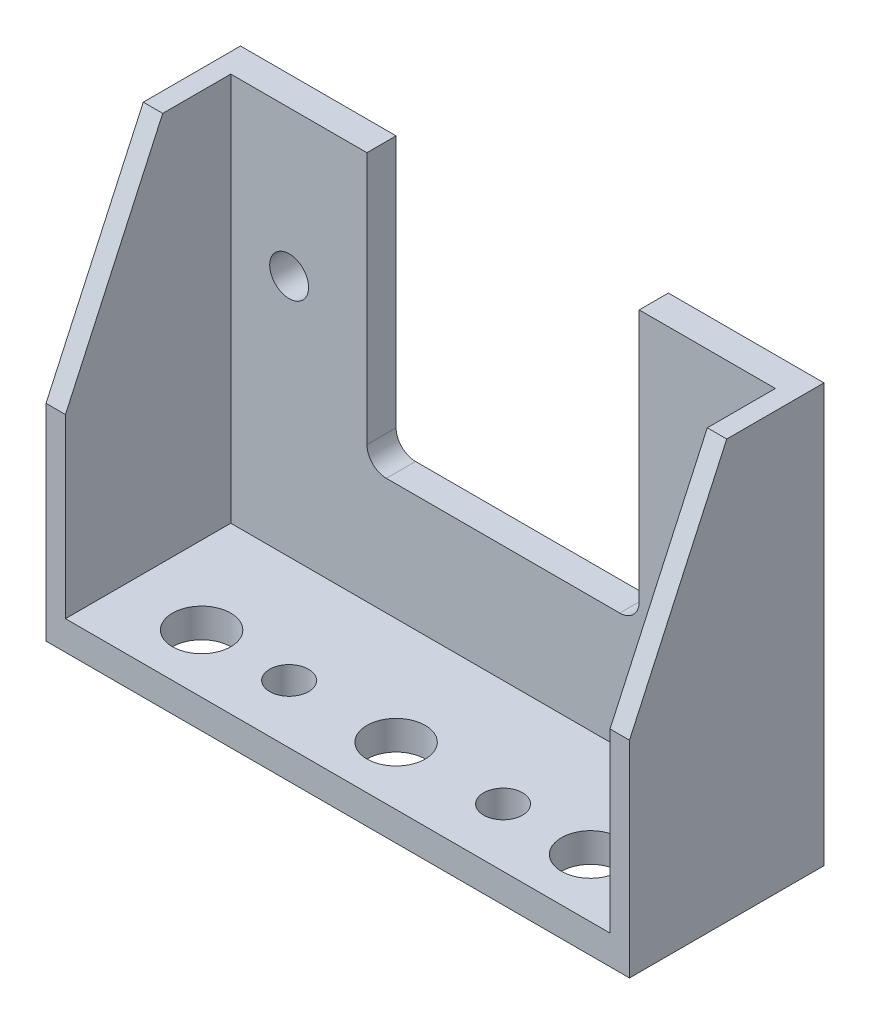
SolidWorks part; units mm, degrees
ref_plane "Front Plane" through (0, 0, 0) normal (0, 0, 1) x (1, 0, 0)
ref_plane "Top Plane" through (0, 0, 0) normal (0, 1, 0) x (1, 0, 0)
ref_plane "Right Plane" through (0, 0, 0) normal (1, 0, 0) x (0, 0, -1)
sketch "Sketch1" plane through (0, 0, 0) normal (0, 1, 0) x (1, 0, 0)
  line L1 (-15, 5) -> (15, 5)
  line L2 (-15, 5) -> (-15, -5)
  line L3 (-15, -5) -> (15, -5)
  line L4 (15, 5) -> (15, -5)
  line L5 (-15, 5) -> (15, -5) construction
  line L6 (-15, -5) -> (15, 5) construction
  circle A0 centre (0, -2) radius 1.5
  point P0 (0, 0)
  dimension "D3" = 3
  dimension "D1" = 30
  dimension "D2" = 10
  dimension "D4" = 3
extrude "Boss-Extrude1" add sketch "Sketch1" along normal mid plane 1.5
sketch "Sketch2" plane through (0, 0.75, 0) normal (0, 1, 0) x (1, 0, 0)
  line L0 (-15, 5) -> (-15, -5) construction
  line L1 (-15, -5) -> (15, -5) construction
  line L2 (0, -0.825) -> (0, 0.825) construction
  circle A0 centre (-10, -2) radius 1.5
  circle A1 centre (10, -2) radius 1.5
  circle A2 centre (-5.5, -2) radius 1
  circle A3 centre (5.5, -2) radius 1
  point P12 (0, 0)
  dimension "D1" = 3
  dimension "D4" = 2
  dimension "D2" = 5
  dimension "D3" = 3
  dimension "D5" = 9.5
extrude "Cut-Extrude1" cut sketch "Sketch2" against normal blind 1.5
sketch "Sketch3" plane through (0, 0, 0) normal (0, 0, 1) x (1, 0, 0)
  line L0 (-15, 0.75) -> (-15, -0.75) construction
  line L1 (15, 20.75) -> (-15, 20.75)
  line L2 (15, 20.75) -> (15, 0.75)
  line L3 (15, 0.75) -> (-15, 0.75)
  line L4 (-15, 20.75) -> (-15, 0.75)
  line L5 (15, 20.75) -> (-15, 0.75) construction
  line L6 (15, 0.75) -> (-15, 20.75) construction
  line L7 (15, 0.75) -> (-15, 0.75) construction
  line L9 (-7, 20.75) -> (7, 20.75)
  line L10 (-7, 20.75) -> (-7, 6.75)
  line L11 (-7, 6.75) -> (7, 6.75)
  line L12 (7, 20.75) -> (7, 6.75)
  point P0 (0, 10.75)
  dimension "D1" = 20
  dimension "D2" = 14
  dimension "D3" = 8
  dimension "D4" = 8
extrude "Boss-Extrude3" add sketch "Sketch3" along normal mid plane 1.5 from offset 4.25 contours L1 L12 L11 L10 L4 L3 L2 offset against normal yes
sketch "Sketch4" plane through (0, 0, 0) normal (0, 0, 1) x (1, 0, 0)
  line L0 (-7, 20.75) -> (-15, 20.75) construction
  line L1 (-15, 20.75) -> (-15, 0.75) construction
  line L2 (0, -5.5) -> (0, 5.5) construction
  circle A0 centre (-11, 13.25) radius 1
  circle A1 centre (11, 13.25) radius 1
  dimension "D1" = 2
  dimension "D2" = 7.5
  dimension "D3" = 4
extrude "Cut-Extrude2" cut sketch "Sketch4" against normal blind 10
fillet "Fillet1" radius 1 2 edges at (7, 6.75, -4.25) (-7, 6.75, -4.25)
sketch "Sketch7" plane through (0, 0, 0) normal (1, 0, 0) x (0, 0, -1)
  line L0 (3.5, 20.75) -> (0, 20.75)
  line L1 (3.5, 20.75) -> (-5, 20.75)
  line L2 (3.5, 20.75) -> (3.5, 0.75)
  line L3 (3.5, 0.75) -> (-5, 0.75)
  line L4 (-5, 20.75) -> (-5, 0.75)
  line L5 (0, 20.75) -> (-5, 9.8401)
extrude "Boss-Extrude4" add sketch "Sketch7" along normal blind 1 from offset 14 contours L0 L5 L4 L3 L2
mirror "Mirror1" about plane through (0, 0, 0) normal (1, 0, 0) of "Boss-Extrude4"
